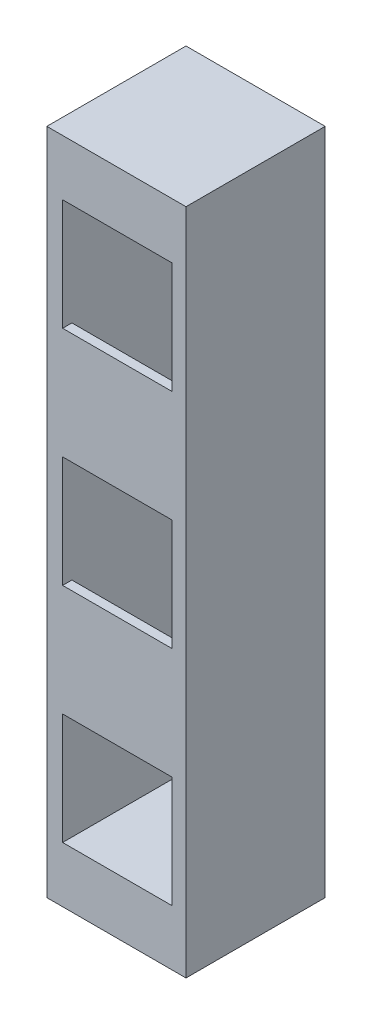
SolidWorks part; units mm, degrees
ref_plane "Alzado" through (0, 0, 0) normal (0, 0, 1) x (1, 0, 0)
ref_plane "Planta" through (0, 0, 0) normal (0, 1, 0) x (1, 0, 0)
ref_plane "Vista lateral" through (0, 0, 0) normal (1, 0, 0) x (0, 0, -1)
sketch "Croquis1" plane through (0, 0, 0) normal (0, 0, 1) x (1, 0, 0)
  line L1 (-95.25, 457.2) -> (95.25, 457.2)
  line L2 (-95.25, 457.2) -> (-95.25, -457.2)
  line L3 (-95.25, -457.2) -> (95.25, -457.2)
  line L4 (95.25, 457.2) -> (95.25, -457.2)
  line L5 (-95.25, 457.2) -> (95.25, -457.2) construction
  line L6 (-95.25, -457.2) -> (95.25, 457.2) construction
  point P0 (0, 0)
  dimension "D1" = 914.4
  dimension "D2" = 190.5
extrude "Saliente-Extruir1" add sketch "Croquis1" along normal mid plane 190.5
sketch "Croquis2" plane through (0, 0, 95.25) normal (0, 0, 1) x (1, 0, 0)
  line L0 (95.25, 457.2) -> (-95.25, 457.2) construction
  line L1 (-76.2, 381) -> (76.2, 381)
  line L2 (-76.2, 381) -> (-76.2, 228.6)
  line L3 (-76.2, 228.6) -> (76.2, 228.6)
  line L4 (76.2, 381) -> (76.2, 228.6)
  line L5 (-73.66, 381) -> (-73.66, 228.6)
  line L6 (-73.66, 381) -> (78.74, 381)
  line L7 (78.74, 381) -> (78.74, 228.6)
  line L8 (-73.66, 228.6) -> (78.74, 228.6)
  line L9 (-73.66, 76.2) -> (-73.66, -76.2)
  line L10 (-73.66, 76.2) -> (78.74, 76.2)
  line L11 (78.74, 76.2) -> (78.74, -76.2)
  line L12 (-73.66, -76.2) -> (78.74, -76.2)
  line L13 (-73.66, -228.6) -> (-73.66, -381)
  line L14 (-73.66, -228.6) -> (78.74, -228.6)
  line L15 (78.74, -228.6) -> (78.74, -381)
  line L16 (-73.66, -381) -> (78.74, -381)
  line L17 (-76.2, 76.2) -> (-76.2, -76.2)
  line L18 (-76.2, 76.2) -> (76.2, 76.2)
  line L19 (76.2, 76.2) -> (76.2, -76.2)
  line L20 (-76.2, -76.2) -> (76.2, -76.2)
  line L21 (-76.2, -228.6) -> (-76.2, -381)
  line L22 (-76.2, -228.6) -> (76.2, -228.6)
  line L23 (76.2, -228.6) -> (76.2, -381)
  line L24 (-76.2, -381) -> (76.2, -381)
  point P4 (0, 381)
  dimension "D1" = 152.4
  dimension "D2" = 152.4
  dimension "D3" = 76.2
  dimension "D5" = 3
  dimension "D4" = 2
extrude "Cortar-Extruir1" cut sketch "Croquis2" against normal blind 177.8 contours L1 L5 L3 L4 | L19 L10 L9 L12 | L23 L14 L13 L16
sketch "Croquis3" plane through (0, 381, 0) normal (0, -1, 0) x (1, 0, 0)
  line L0 (-73.66, 82.55) -> (76.2, 82.55)
  line L4 (76.2, 95.25) -> (-73.66, 95.25)
  line L5 (-73.66, 95.25) -> (-73.66, -82.55)
  line L6 (-73.66, -82.55) -> (76.2, -82.55)
  line L7 (76.2, -82.55) -> (76.2, 95.25)
  line L9 (-73.66, 82.55) -> (-73.66, -82.55)
  line L10 (-73.66, -82.55) -> (76.2, -82.55)
  line L11 (76.2, -82.55) -> (76.2, 82.55)
  dimension "D2" = 165.1
  dimension "D1" = 0
extrude "Cortar-Extruir3" cut sketch "Croquis3" along normal up to vertex
